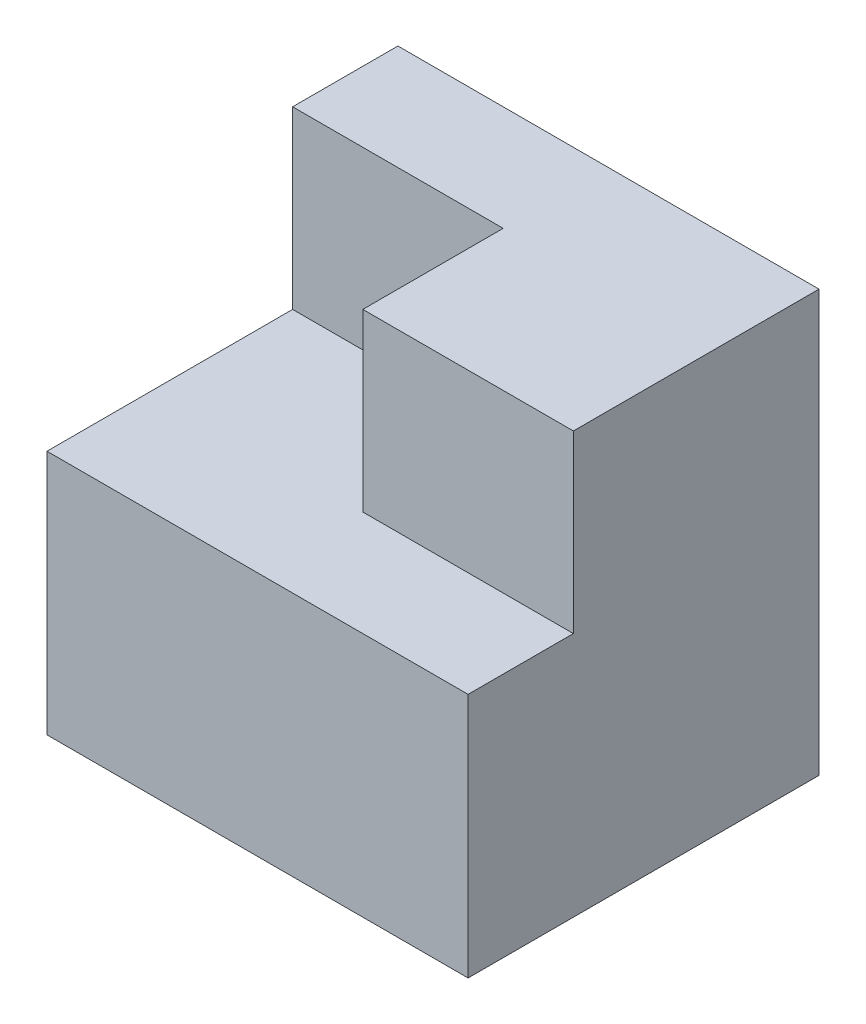
SolidWorks part; units mm, degrees
ref_plane "Front Plane" through (0, 0, 0) normal (0, 0, 1) x (1, 0, 0)
ref_plane "Top Plane" through (0, 0, 0) normal (0, 1, 0) x (1, 0, 0)
ref_plane "Right Plane" through (0, 0, 0) normal (1, 0, 0) x (0, 0, -1)
sketch "Sketch1" plane through (0, 0, 0) normal (0, 1, 0) x (1, 0, 0)
  line L1 (-3, -2.5) -> (3, -2.5)
  line L2 (-3, -2.5) -> (-3, 2.5)
  line L3 (-3, 2.5) -> (3, 2.5)
  line L4 (3, -2.5) -> (3, 2.5)
  line L5 (-3, -2.5) -> (3, 2.5) construction
  line L6 (-3, 2.5) -> (3, -2.5) construction
  point P0 (0, 0)
  dimension "D1" = 5
  dimension "D2" = 6
extrude "Boss-Extrude1" add sketch "Sketch1" along normal blind 6
sketch "Sketch2" plane through (0, 6, 0) normal (0, 1, 0) x (1, 0, 0)
  line L0 (3, -1) -> (0, -1)
  line L1 (3, -2.5) -> (3, 2.5) construction
  line L2 (0, -1) -> (0, 1)
  line L3 (0, 1) -> (-3, 1)
  line L4 (-3, 2.5) -> (-3, -2.5) construction
  line L5 (-3, 1) -> (-3, -2.5)
  line L6 (-3, -2.5) -> (3, -2.5)
  line L7 (3, -2.5) -> (3, -1)
  dimension "D1" = 1.5
  dimension "D2" = 3.5
  dimension "D3" = 3
extrude "Cut-Extrude1" cut sketch "Sketch2" against normal blind 2.5
